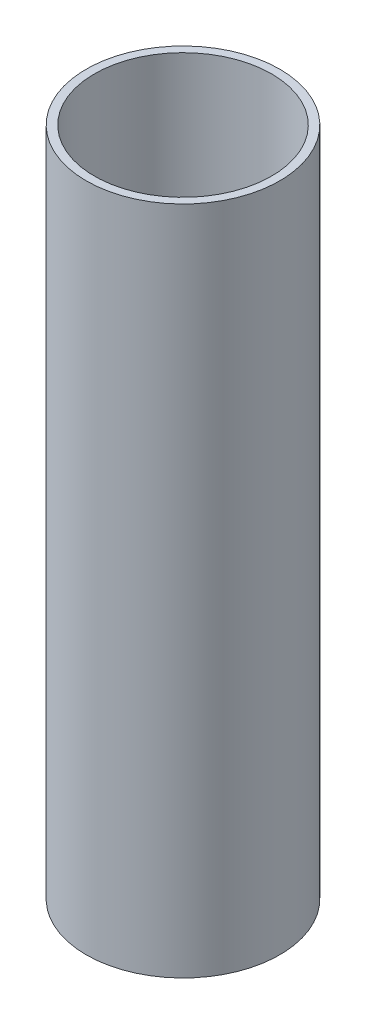
SolidWorks part; units mm, degrees
ref_plane "Front Plane" through (0, 0, 0) normal (0, 0, 1) x (1, 0, 0)
ref_plane "Top Plane" through (0, 0, 0) normal (0, 1, 0) x (1, 0, 0)
ref_plane "Right Plane" through (0, 0, 0) normal (1, 0, 0) x (0, 0, -1)
sketch "Croquis1" plane through (0, 0, 0) normal (1, 0, 0) x (0, 0, -1)
  line L0 (0, 0) -> (0, 98.0232) construction
  line L1 (21.15, 0) -> (23.1, 0)
  line L2 (21.15, 0) -> (21.15, 160)
  line L3 (21.15, 160) -> (23.1, 160)
  line L4 (23.1, 0) -> (23.1, 160)
  dimension "D3" = 160
  dimension "D1" = 46.2
  dimension "D2" = 42.3
revolve "Revolución1" add sketch "Croquis1" angle 360 about L0
equation "\"OD\" = 46.2"
equation "\"Pared\"= 8"
equation "\"Altura\"=160"
equation "\"D3@Croquis1\"=\"Altura\""
equation "\"D1@Croquis1\"=\"OD\""
